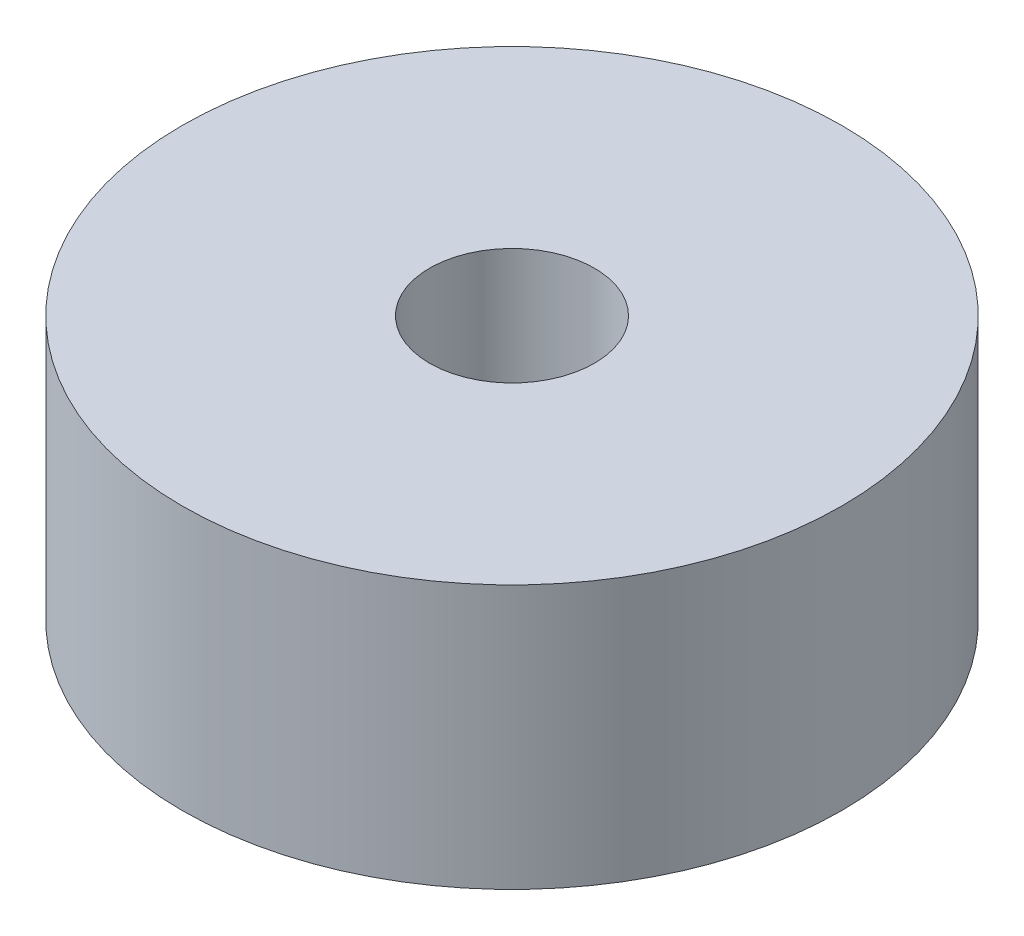
SolidWorks part; units mm, degrees
ref_plane "Alzado" through (0, 0, 0) normal (0, 0, 1) x (1, 0, 0)
ref_plane "Planta" through (0, 0, 0) normal (0, 1, 0) x (1, 0, 0)
ref_plane "Vista lateral" through (0, 0, 0) normal (1, 0, 0) x (0, 0, -1)
sketch "Croquis1" plane through (0, 0, 0) normal (0, 1, 0) x (1, 0, 0)
  circle A0 centre (0, 0) radius 25.4
  circle A1 centre (0, 0) radius 6.35
  dimension "D1" = 50.8
  dimension "D2" = 12.7
extrude "Saliente-Extruir1" add sketch "Croquis1" along normal blind 20.32
